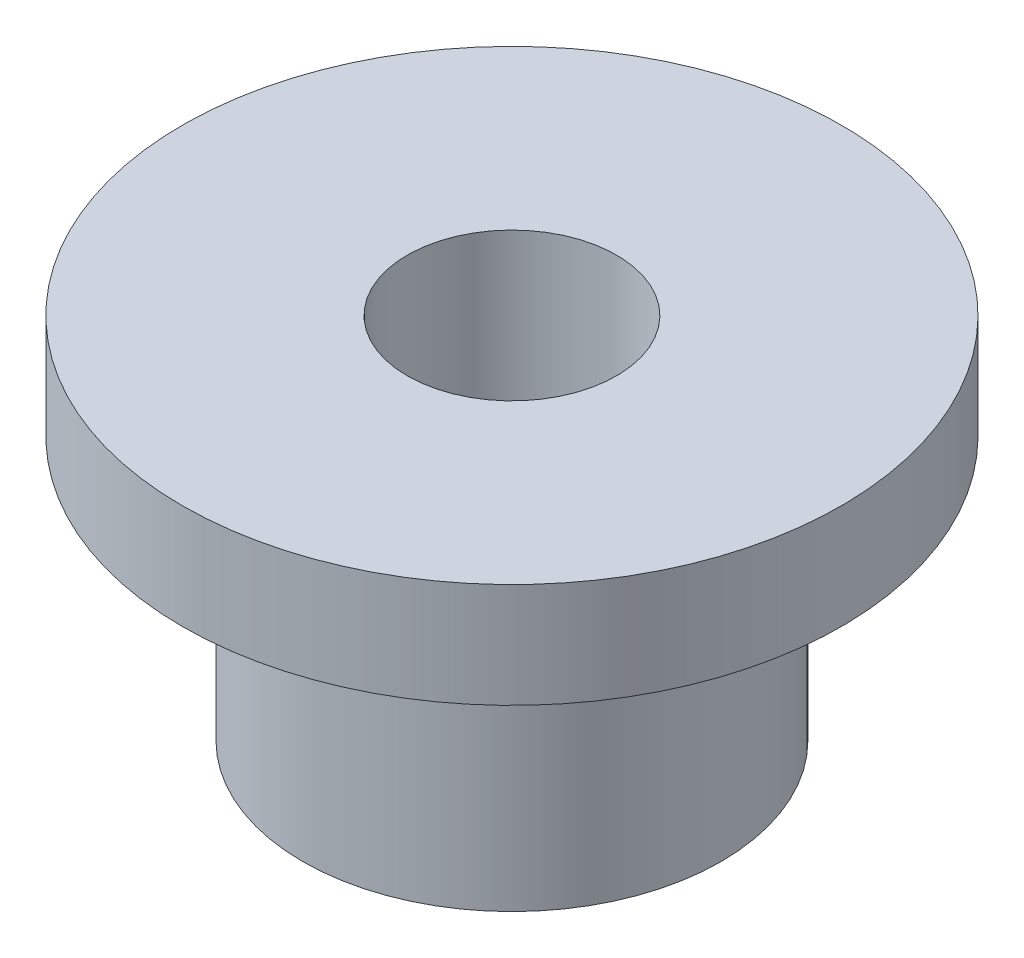
SolidWorks part; units mm, degrees
material "ABS"
ref_plane "Front Plane" through (0, 0, 0) normal (0, 0, 1) x (1, 0, 0)
ref_plane "Top Plane" through (0, 0, 0) normal (0, 1, 0) x (1, 0, 0)
ref_plane "Right Plane" through (0, 0, 0) normal (1, 0, 0) x (0, 0, -1)
sketch "Sketch1" plane through (0, 0, 0) normal (0, 1, 0) x (1, 0, 0)
  circle A0 centre (0, 0) radius 6.35
  circle A1 centre (0, 0) radius 3.175
  dimension "D1" = 6.35
  dimension "D2" = 12.7
extrude "Boss-Extrude1" add sketch "Sketch1" along normal blind 8
sketch "Sketch2" plane through (0, 8, 0) normal (0, 1, 0) x (1, 0, 0)
  circle A0 centre (0, 0) radius 3.175
  circle A1 centre (0, 0) radius 10
  circle A2 centre (0, 0) radius 3.175 construction
  dimension "D1" = 20
extrude "Boss-Extrude2" add sketch "Sketch2" along normal blind 3.175
